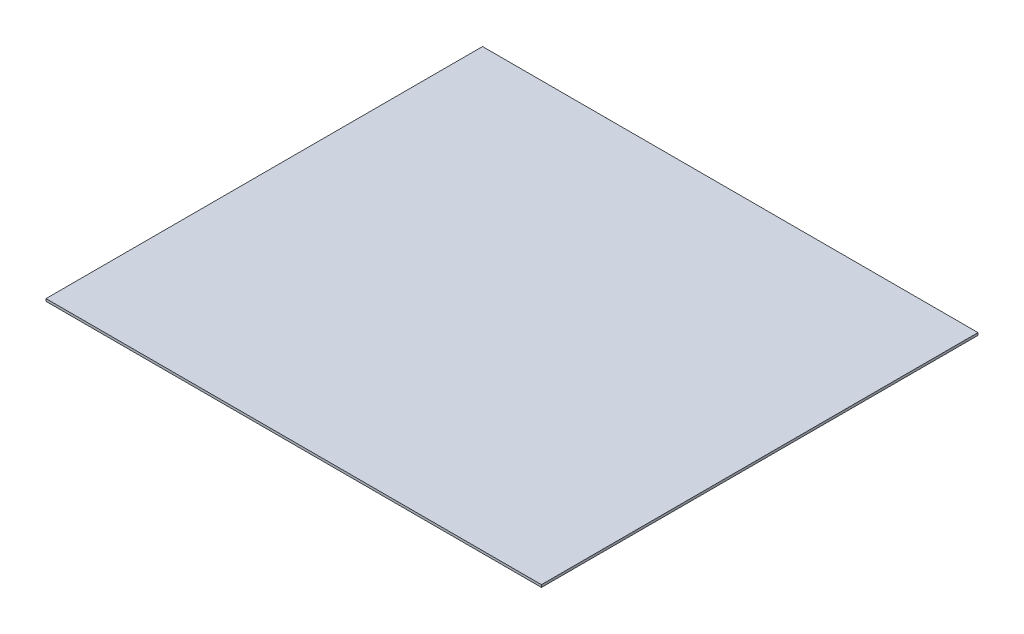
SolidWorks part; units mm, degrees
material "Pine"
ref_plane "Front Plane" through (0, 0, 0) normal (0, 0, 1) x (1, 0, 0)
ref_plane "Top Plane" through (0, 0, 0) normal (0, 1, 0) x (1, 0, 0)
ref_plane "Right Plane" through (0, 0, 0) normal (1, 0, 0) x (0, 0, -1)
sketch "Sketch1" plane through (0, 0, 0) normal (0, 1, 0) x (1, 0, 0)
  line L1 (-1282.7, -1130.173) -> (1282.7, -1130.173)
  line L2 (-1282.7, -1130.173) -> (-1282.7, 1130.173)
  line L3 (-1282.7, 1130.173) -> (1282.7, 1130.173)
  line L4 (1282.7, -1130.173) -> (1282.7, 1130.173)
  line L5 (-1282.7, -1130.173) -> (1282.7, 1130.173) construction
  line L6 (-1282.7, 1130.173) -> (1282.7, -1130.173) construction
  point P0 (0, 0)
  dimension "D1" = 2565.4
  dimension "D2" = 2260.346
extrude "Boss-Extrude1" add sketch "Sketch1" along normal blind 12.7
